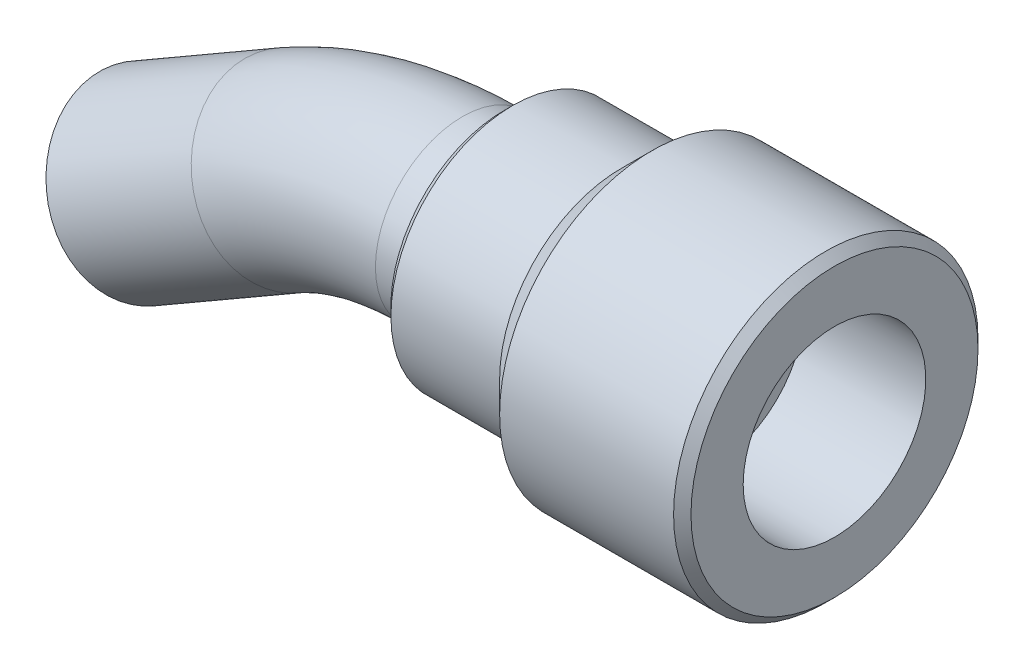
SolidWorks part; units mm, degrees
ref_plane "Front Plane" through (0, 0, 0) normal (0, 0, 1) x (1, 0, 0)
ref_plane "Top Plane" through (0, 0, 0) normal (0, 1, 0) x (1, 0, 0)
ref_plane "Right Plane" through (0, 0, 0) normal (1, 0, 0) x (0, 0, -1)
sketch "Sketch1" plane through (0, 0, 0) normal (0, 0, 1) x (1, 0, 0)
  line L0 (0, 0) -> (18.9142, 0) construction
  line L1 (0, 10) -> (0, 14)
  line L2 (0, 14) -> (13.5, 14)
  line L3 (13.5, 14) -> (17, 17.5)
  line L4 (17, 17.5) -> (38, 17.5)
  line L5 (38, 17.5) -> (38, 10.5)
  line L6 (38, 10.5) -> (24, 10.5)
  line L7 (24, 10.5) -> (24, 6)
  line L8 (24, 6) -> (14.5, 6)
  line L9 (14.5, 6) -> (14.5, 10)
  line L10 (14.5, 10) -> (0, 10)
  dimension "D1" = 10
  dimension "D2" = 10.5
  dimension "D3" = 4
  dimension "D4" = 14.5
  dimension "D5" = 14
  dimension "D6" = 38
  dimension "D7" = 4
  dimension "D8" = 135
  dimension "D9" = 1
  dimension "D10" = 7
revolve "Revolve1" add sketch "Sketch1" angle 360 about L0
chamfer "Chamfer1" distance 1 angle 45 2 edges at (38, 0, 17.5) (0, 0, 14)
sketch "Sketch2" plane through (14.5, 0, 0) normal (-1, 0, 0) x (0, 0, 1)
  circle A0 centre (0, 0) radius 6 construction
  circle A1 centre (0, 0) radius 10
  circle A2 centre (0, 0) radius 10
  circle A3 centre (0, 0) radius 6
  dimension "D1" = 0
sketch "Sketch3" plane through (0, 0, 0) normal (0, 0, 1) x (1, 0, 0)
  line L0 (14.5, 0) -> (-4.782, 0)
  line L2 (-24.782, -5.359) -> (-41.4808, -15)
  line L3 (14.5, 10) -> (14.5, -10) construction
  arc A0 (-4.782, 0) -> (-24.782, -5.359) centre (-4.782, -40) ccw
  point P2 (14.5, 0)
  point P8 (-15.5, 0)
  point P9 (13.5, 0)
  dimension "D4" = 40
  dimension "D1" = 30
  dimension "D2" = 30
  dimension "D3" = 150
sweep "Sweep6" add profiles "Sketch2" path "Sketch3"
